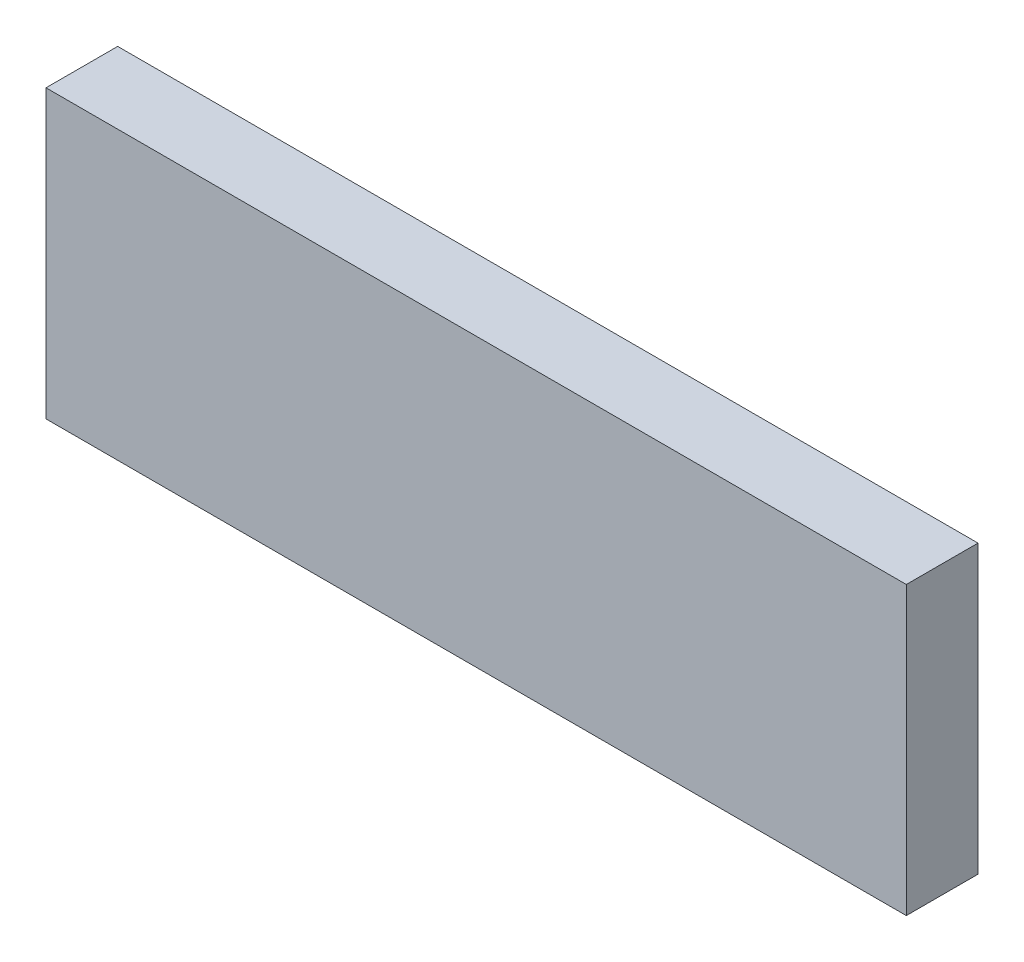
SolidWorks part; units mm, degrees
ref_plane "Front Plane" through (0, 0, 0) normal (0, 0, 1) x (1, 0, 0)
ref_plane "Top Plane" through (0, 0, 0) normal (0, 1, 0) x (1, 0, 0)
ref_plane "Right Plane" through (0, 0, 0) normal (1, 0, 0) x (0, 0, -1)
sketch "Sketch1" plane through (0, 0, 0) normal (0, 0, 1) x (1, 0, 0)
  line L1 (-60, -20) -> (60, -20)
  line L2 (-60, -20) -> (-60, 20)
  line L3 (-60, 20) -> (60, 20)
  line L4 (60, -20) -> (60, 20)
  line L5 (-60, -20) -> (60, 20) construction
  line L6 (-60, 20) -> (60, -20) construction
  point P0 (0, 0)
  dimension "D1" = 120
  dimension "D2" = 40
extrude "Boss-Extrude1" add sketch "Sketch1" along normal blind 10
